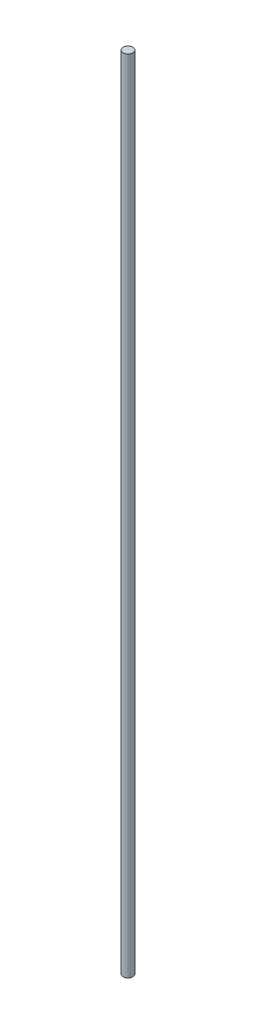
SolidWorks part; units mm, degrees
ref_plane "Front Plane" through (0, 0, 0) normal (0, 0, 1) x (1, 0, 0)
ref_plane "Top Plane" through (0, 0, 0) normal (0, 1, 0) x (1, 0, 0)
ref_plane "Right Plane" through (0, 0, 0) normal (1, 0, 0) x (0, 0, -1)
sketch "Sketch1" plane through (0, 0, 0) normal (0, 1, 0) x (1, 0, 0)
  circle A0 centre (0, 0) radius 1.5
  dimension "D1" = 3
extrude "Boss-Extrude1" add sketch "Sketch1" along normal blind 245
